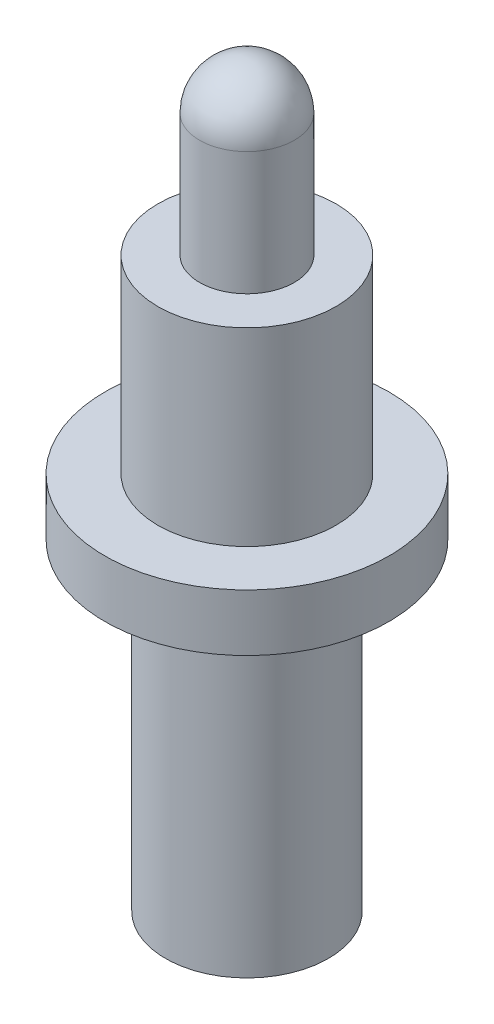
SolidWorks part; units mm, degrees
material "Copper"
ref_plane "Front Plane" through (0, 0, 0) normal (0, 0, 1) x (1, 0, 0)
ref_plane "Top Plane" through (0, 0, 0) normal (0, 1, 0) x (1, 0, 0)
ref_plane "Right Plane" through (0, 0, 0) normal (1, 0, 0) x (0, 0, -1)
sketch "Sketch1" plane through (0, 0, 0) normal (1, 0, 0) x (0, 0, -1)
  line L0 (0, 0) -> (0, 56.8505) construction
  line L1 (0.635, 7.62) -> (1.1938, 7.62)
  line L2 (1.1938, 7.62) -> (1.1938, 5.08)
  line L3 (1.1938, 5.08) -> (1.905, 5.08)
  line L4 (1.905, 5.08) -> (1.905, 4.318)
  line L5 (1.905, 4.318) -> (1.0922, 4.318)
  line L6 (1.0922, 4.318) -> (1.0922, 0)
  line L7 (1.0922, 0) -> (0, 0)
  line L8 (0.635, 7.62) -> (0.635, 9.271)
  line L9 (0, 9.906) -> (0, 0)
  arc A0 (0.635, 9.271) -> (0, 9.906) centre (0, 9.271) ccw
  dimension "D1" = 2.1844
  dimension "D2" = 2.3876
  dimension "D3" = 3.81
  dimension "D4" = 0.762
  dimension "D5" = 4.318
  dimension "D6" = 7.62
  dimension "D7" = 2.286
  dimension "D8" = 1.27
revolve "Revolve1" add sketch "Sketch1" angle 360 about L0
ref_plane "Plane1" through (0, 9.906, 0) normal (0, -1, 0) x (1, 0, 0)
